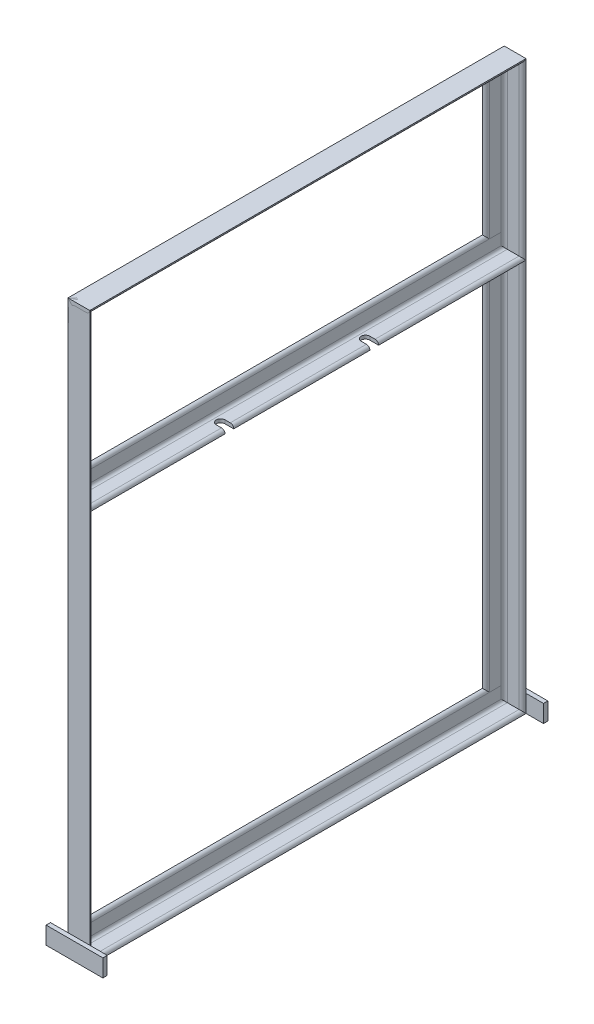
SolidWorks part; units mm, degrees
material "1060 Alloy"
ref_plane "Front Plane" through (0, 0, 0) normal (0, 0, 1) x (1, 0, 0)
ref_plane "Top Plane" through (0, 0, 0) normal (0, 1, 0) x (1, 0, 0)
ref_plane "Right Plane" through (0, 0, 0) normal (1, 0, 0) x (0, 0, -1)
sketch "Sketch1" plane through (0, 0, 0) normal (1, 0, 0) x (0, 0, -1)
  line L1 (468.8789, 50) -> (468.8789, 500)
  line L2 (468.8789, 700) -> (-31.1211, 700)
  line L3 (-31.1211, 700) -> (-31.1211, 50)
  line L5 (-31.1211, 500) -> (468.8789, 500)
  line L6 (468.8789, 500) -> (468.8789, 700)
  line L7 (-31.1211, 50) -> (468.8789, 50)
  dimension "D3" = 500
  dimension "D5" = 200
other "Structural Member4"
ref_plane "Plane4" through (0, 700, -468.8789) normal (0, 0, 1) x (0, -1, 0)
sketch "Sketch14" plane through (0, 700, -468.8789) normal (0, 0, 1) x (0, -1, 0)
  line L0 (0, 0) -> (0, 25)
  line L1 (0, 12.5) -> (4, 12.5) construction
  line L2 (4, 21) -> (4, 7.5)
  line L3 (7.5, 4) -> (21, 4)
  line L4 (12.5, 4) -> (12.5, 0) construction
  line L5 (25, 0) -> (0, 0)
  arc A0 (25, 0) -> (21, 4) centre (21, 0) ccw
  arc A1 (0, 25) -> (4, 21) centre (0, 21) cw
  arc A2 (7.5, 4) -> (4, 7.5) centre (7.5, 7.5) cw
  point P10 (12.5, 0)
  point P14 (0, 12.5)
  point P15 (4, 12.5)
  point P16 (12.5, 4)
  point P17 (4, 25)
  point P18 (25, 4)
  point P21 (0, 0)
  dimension "D2" = 4
  dimension "D3" = 25
  dimension "Radius_1" = 3.5
  dimension "D1" = 4
other "Structural Member5"
ref_plane "Plane5" through (0, 500, 31.1211) normal (0, 0, -1) x (0, 1, 0)
sketch "Sketch15" plane through (0, 500, 31.1211) normal (0, 0, -1) x (0, 1, 0)
  line L0 (0, 0) -> (0, 25)
  line L1 (0, 12.5) -> (4, 12.5) construction
  line L2 (4, 21) -> (4, 7.5)
  line L3 (7.5, 4) -> (21, 4)
  line L4 (12.5, 4) -> (12.5, 0) construction
  line L5 (25, 0) -> (0, 0)
  arc A0 (25, 0) -> (21, 4) centre (21, 0) ccw
  arc A1 (0, 25) -> (4, 21) centre (0, 21) cw
  arc A2 (7.5, 4) -> (4, 7.5) centre (7.5, 7.5) cw
  point P10 (12.5, 0)
  point P14 (0, 12.5)
  point P15 (4, 12.5)
  point P16 (12.5, 4)
  point P17 (4, 25)
  point P18 (25, 4)
  point P21 (0, 0)
  dimension "D2" = 4
  dimension "D3" = 25
  dimension "Radius_1" = 3.5
  dimension "D1" = 4
sketch "Sketch23" plane through (0, 500, 0) normal (0, -1, 0) x (-1, 0, 0)
  line L0 (-25, 468.8789) -> (-25, -31.1211) construction
  line L1 (-25, 123.8789) -> (-15, 123.8789)
  line L2 (-25, 123.8789) -> (-25, 133.8789)
  line L3 (-25, 133.8789) -> (-15, 133.8789)
  line L4 (-25, -31.1211) -> (0, -31.1211) construction
  arc A0 (-15, 123.8789) -> (-15, 133.8789) centre (-15, 128.8789) ccw
  dimension "D1" = 10
  dimension "D2" = 10
  dimension "D3" = 160
extrude "Cut-Extrude3" cut sketch "Sketch23" against normal blind 5
pattern_linear "LPattern2" count 2 spacing 166 along (0, 0, -1) of "Cut-Extrude3"
sketch "Sketch27" plane through (0, 0, 0) normal (-1, 0, 0) x (0, 0, 1)
other "Structural Member7"
ref_plane "Plane10" through (0, 50, 31.1211) normal (0, 0, -1) x (0, 1, 0)
sketch "Sketch110" plane through (0, 50, 31.1211) normal (0, 0, -1) x (0, 1, 0)
  line L0 (0, 0) -> (0, 25)
  line L1 (0, 12.5) -> (4, 12.5) construction
  line L2 (4, 21) -> (4, 7.5)
  line L3 (7.5, 4) -> (21, 4)
  line L4 (12.5, 4) -> (12.5, 0) construction
  line L5 (25, 0) -> (0, 0)
  arc A0 (25, 0) -> (21, 4) centre (21, 0) ccw
  arc A1 (0, 25) -> (4, 21) centre (0, 21) cw
  arc A2 (7.5, 4) -> (4, 7.5) centre (7.5, 7.5) cw
  point P10 (12.5, 0)
  point P14 (0, 12.5)
  point P15 (4, 12.5)
  point P16 (12.5, 4)
  point P17 (4, 25)
  point P18 (25, 4)
  point P21 (0, 0)
  dimension "D2" = 4
  dimension "D3" = 25
  dimension "Radius_1" = 3.5
  dimension "D1" = 4
other "Structural Member8"
ref_plane "Plane11" through (0, 700, 31.1211) normal (0, -1, 0) x (0, 0, -1)
sketch "Sketch111" plane through (0, 700, 31.1211) normal (0, -1, 0) x (0, 0, -1)
  line L0 (0, 0) -> (0, 25)
  line L1 (0, 12.5) -> (4, 12.5) construction
  line L2 (4, 21) -> (4, 7.5)
  line L3 (7.5, 4) -> (21, 4)
  line L4 (12.5, 4) -> (12.5, 0) construction
  line L5 (25, 0) -> (0, 0)
  arc A0 (25, 0) -> (21, 4) centre (21, 0) ccw
  arc A1 (0, 25) -> (4, 21) centre (0, 21) cw
  arc A2 (7.5, 4) -> (4, 7.5) centre (7.5, 7.5) cw
  point P10 (12.5, 0)
  point P14 (0, 12.5)
  point P15 (4, 12.5)
  point P16 (12.5, 4)
  point P17 (4, 25)
  point P18 (25, 4)
  point P21 (0, 0)
  dimension "D2" = 4
  dimension "D3" = 25
  dimension "Radius_1" = 3.5
  dimension "D1" = 4
other "Structural Member9"
ref_plane "Plane12" through (0, 50, -468.8789) normal (0, 1, 0) x (0, 0, 1)
sketch "Sketch112" plane through (0, 50, -468.8789) normal (0, 1, 0) x (0, 0, 1)
  line L0 (0, 0) -> (0, 25)
  line L1 (0, 12.5) -> (4, 12.5) construction
  line L2 (4, 21) -> (4, 7.5)
  line L3 (7.5, 4) -> (21, 4)
  line L4 (12.5, 4) -> (12.5, 0) construction
  line L5 (25, 0) -> (0, 0)
  arc A0 (25, 0) -> (21, 4) centre (21, 0) ccw
  arc A1 (0, 25) -> (4, 21) centre (0, 21) cw
  arc A2 (7.5, 4) -> (4, 7.5) centre (7.5, 7.5) cw
  point P10 (12.5, 0)
  point P14 (0, 12.5)
  point P15 (4, 12.5)
  point P16 (12.5, 4)
  point P17 (4, 25)
  point P18 (25, 4)
  point P21 (0, 0)
  dimension "D2" = 4
  dimension "D3" = 25
  dimension "Radius_1" = 3.5
  dimension "D1" = 4
other "Structural Member10"
ref_plane "Plane13" through (0, 500, -468.8789) normal (0, 1, 0) x (0, 0, 1)
sketch "Sketch113" plane through (0, 500, -468.8789) normal (0, 1, 0) x (0, 0, 1)
  line L0 (0, 0) -> (0, 25)
  line L1 (0, 12.5) -> (4, 12.5) construction
  line L2 (4, 21) -> (4, 7.5)
  line L3 (7.5, 4) -> (21, 4)
  line L4 (12.5, 4) -> (12.5, 0) construction
  line L5 (25, 0) -> (0, 0)
  arc A0 (25, 0) -> (21, 4) centre (21, 0) ccw
  arc A1 (0, 25) -> (4, 21) centre (0, 21) cw
  arc A2 (7.5, 4) -> (4, 7.5) centre (7.5, 7.5) cw
  point P10 (12.5, 0)
  point P14 (0, 12.5)
  point P15 (4, 12.5)
  point P16 (12.5, 4)
  point P17 (4, 25)
  point P18 (25, 4)
  point P21 (0, 0)
  dimension "D2" = 4
  dimension "D3" = 25
  dimension "Radius_1" = 3.5
  dimension "D1" = 4
sketch "Sketch114" plane through (0, 0, 31.1211) normal (0, 0, 1) x (1, 0, 0)
  line L0 (0, 50) -> (0, 75) construction
  line L1 (-20, 50) -> (45, 50)
  line L2 (-20, 50) -> (-20, 70)
  line L3 (-20, 70) -> (45, 70)
  line L4 (45, 50) -> (45, 70)
  dimension "D1" = 20
  dimension "D2" = 65
  dimension "D3" = 20
extrude "Boss-Extrude6" add sketch "Sketch114" along normal blind 5 separate body
sketch "Sketch115" plane through (0, 0, -468.8789) normal (0, 0, -1) x (-1, 0, 0)
  line L0 (-25, 500) -> (-25, 50) construction
  line L1 (20, 50) -> (-45, 50)
  line L2 (20, 50) -> (20, 70)
  line L3 (20, 70) -> (-45, 70)
  line L4 (-45, 50) -> (-45, 70)
  dimension "D1" = 20
  dimension "D2" = 65
  dimension "D3" = 20
extrude "Boss-Extrude7" add sketch "Sketch115" along normal blind 5 separate body
